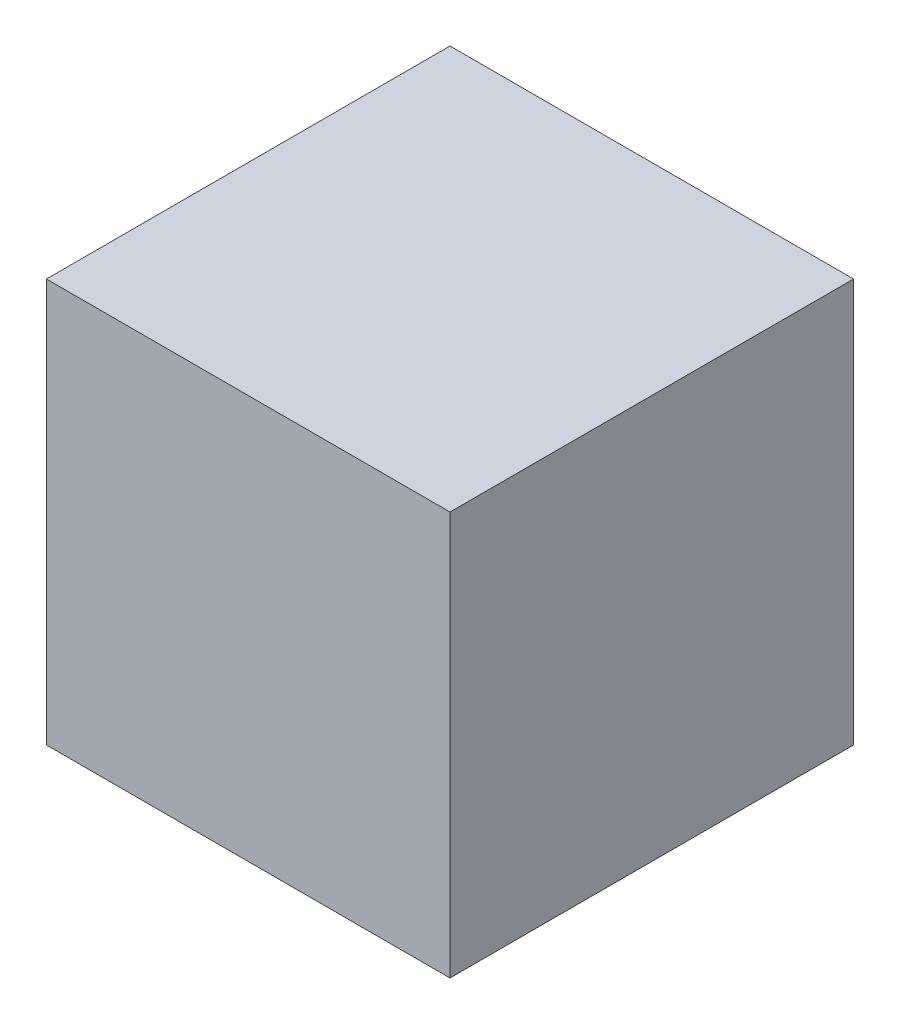
SolidWorks part; units mm, degrees
ref_plane "Front Plane" through (0, 0, 0) normal (0, 0, 1) x (1, 0, 0)
ref_plane "Top Plane" through (0, 0, 0) normal (0, 1, 0) x (1, 0, 0)
ref_plane "Right Plane" through (0, 0, 0) normal (1, 0, 0) x (0, 0, -1)
sketch "Sketch1" plane through (0, 0, 0) normal (0, 1, 0) x (1, 0, 0)
  line L1 (-50, -50) -> (50, -50)
  line L2 (-50, -50) -> (-50, 50)
  line L3 (-50, 50) -> (50, 50)
  line L4 (50, -50) -> (50, 50)
  line L5 (-50, -50) -> (50, 50) construction
  line L6 (-50, 50) -> (50, -50) construction
  point P0 (0, 0)
  dimension "D1" = 100
extrude "Boss-Extrude1" add sketch "Sketch1" along normal mid plane 100
